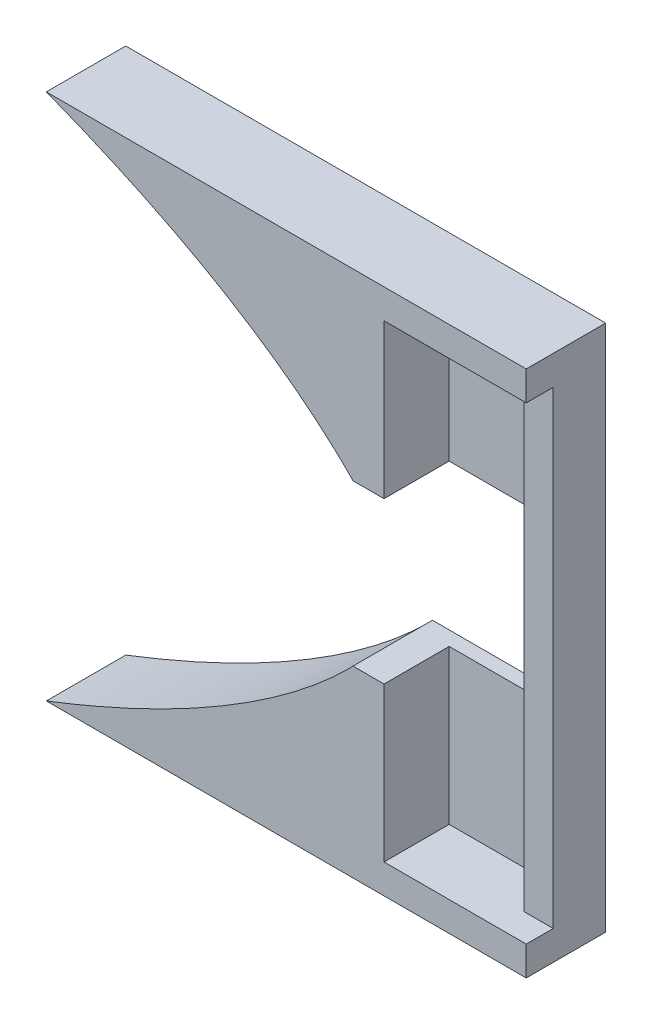
SolidWorks part; units mm, degrees
ref_plane "Front Plane" through (0, 0, 0) normal (0, 0, 1) x (1, 0, 0)
ref_plane "Top Plane" through (0, 0, 0) normal (0, 1, 0) x (1, 0, 0)
ref_plane "Right Plane" through (0, 0, 0) normal (1, 0, 0) x (0, 0, -1)
sketch "Sketch1" plane through (0, 0, 0) normal (0, 0, 1) x (1, 0, 0)
  line L0 (-3.952, 0) -> (4.2326, 0) construction
  line L1 (0, 24) -> (0, -24)
  line L2 (0, 24) -> (0, -24)
  line L3 (63, 14.75) -> (63.35, 14.75) construction
  line L4 (38.2956, -15.1) -> (63.35, -15.1)
  line L5 (38.2956, -15.1) -> (38.2956, 15.1)
  line L6 (38.2956, 15.1) -> (63.35, 15.1)
  line L7 (63.35, -15.1) -> (63.35, 15.1)
  line L8 (38.2956, -15.1) -> (63.35, 15.1) construction
  line L9 (38.2956, 15.1) -> (63.35, -15.1) construction
  line L10 (63, 14.75) -> (63, 15.1) construction
  line L11 (55.9, 5.05) -> (55.9, -5.05)
  line L12 (55.9, 14.75) -> (55.9, 5.05)
  line L13 (55.9, 5.05) -> (59.2, 5.05)
  line L14 (59.2, 5.05) -> (60.45, 5.05)
  line L15 (60.45, 5.05) -> (60.45, -5.05)
  line L16 (60.45, -5.05) -> (59.2, -5.05)
  line L17 (59.2, -5.05) -> (55.9, -5.05)
  line L18 (55.9, -5.05) -> (55.9, -14.75)
  line L19 (55.9, -14.75) -> (63, -14.75)
  line L20 (63, -14.75) -> (63, 14.75)
  line L21 (63, 14.75) -> (55.9, 14.75)
  line L22 (55.9, 14.75) -> (55.9, 5.05)
  line L23 (55.9, 5.05) -> (59.2, 5.05)
  line L24 (59.2, 5.05) -> (60.45, 5.05)
  line L25 (60.45, 5.05) -> (60.45, -5.05)
  line L26 (60.45, -5.05) -> (59.2, -5.05)
  line L27 (59.2, -5.05) -> (55.9, -5.05)
  line L28 (55.9, -5.05) -> (55.9, -14.75)
  line L29 (55.9, -14.75) -> (63, -14.75)
  line L30 (63, -14.75) -> (63, 14.75)
  line L31 (63, 14.75) -> (55.9, 14.75)
  line L32 (63.35, 15.1) -> (64.85, 15.1) construction
  line L33 (55.9, 5.05) -> (53.945, 5.05)
  line L34 (55.9, 5.05) -> (55.9, -5.05)
  line L35 (55.9, -5.05) -> (53.945, -5.05)
  line L36 (53.945, 5.05) -> (53.945, -5.05)
  line L37 (34.6449, -16.6) -> (64.85, -16.6)
  line L38 (34.6449, -16.6) -> (34.6449, 16.6)
  line L39 (34.6449, 16.6) -> (64.85, 16.6)
  line L40 (64.85, -16.6) -> (64.85, 16.6)
  line L41 (34.6449, -16.6) -> (64.85, 16.6) construction
  line L42 (34.6449, 16.6) -> (64.85, -16.6) construction
  line L43 (63.35, 15.1) -> (63.35, 16.6) construction
  arc A1 (53.7033, -5.3033) -> (53.7033, 5.3033) centre (48.4, 0) ccw
  arc A2 (53.7033, -5.3033) -> (53.7033, 5.3033) centre (48.4, 0) ccw
  spline S2 degree 3 poles (-39742.6829, -3603.7041) (40725.6647, 1982.9369) (-40729.1405, -551.1643) (39971.9091, -538.7658) knots -9.910331 -9.910331 -9.910331 -9.910331 10.871093 10.871093 10.871093 10.871093 only from (53.7033, 5.3033) to (0, 24)
  spline S3 degree 3 poles (39973.8727, 538.7655) (-40730.5107, 551.2054) (40726.4161, -1982.9853) (-39742.8292, 3603.7143) knots -9.871262 -9.871262 -9.871262 -9.871262 10.910344 10.910344 10.910344 10.910344 only from (0, -24) to (53.7033, -5.3033)
  spline S4 degree 3 poles (53.7033, 5.3033) (40.8426, 18.164) (10.9049, 24) (0, 24) knots 0 0 0 0 1 1 1 1
  spline S5 degree 3 poles (0, -24) (10.9049, -24) (40.8426, -18.164) (53.7033, -5.3033) knots 0 0 0 0 1 1 1 1
  point P16 (50.8228, 0)
  point P28 (49.7474, 0)
  dimension "D3" = 0.35
  dimension "D4" = 1.5
  dimension "D1" = 0
  dimension "D2" = 0
extrude "Boss-Extrude1" add sketch "Sketch1" against normal blind 3.3 contours S5 L4 L7 L6 S4 A2 L31 L30 L29 L28 L27 L26 L25 L24 L23 L22 | S5 L37 L40 L39 S4 L6 L7 L4
sketch "Sketch2" plane through (0, 0, -3.3) normal (0, 0, -1) x (-1, 0, 0)
  line L0 (-63, -14.75) -> (-63, 14.75) construction
  line L1 (-55.9, -14.75) -> (-63, -14.75)
  line L2 (-55.9, -14.75) -> (-55.9, -5.05)
  line L3 (-55.9, -5.05) -> (-63, -5.05)
  line L4 (-63, -14.75) -> (-63, -5.05)
  line L5 (-55.9, -5.05) -> (-53.945, -5.05) construction
  line L6 (-55.9, 5.05) -> (-53.945, 5.05) construction
  line L7 (-55.9, 14.75) -> (-63, 14.75)
  line L8 (-55.9, 14.75) -> (-55.9, 5.05)
  line L9 (-55.9, 5.05) -> (-63, 5.05)
  line L10 (-63, 14.75) -> (-63, 5.05)
extrude "Boss-Extrude2" add sketch "Sketch2" against normal blind 0.9
sketch "Sketch3" plane through (0, 0, 0) normal (0, 0, 1) x (1, 0, 0)
  line L0 (63, 14.75) -> (64.85, 14.75)
  line L1 (63, -14.75) -> (64.85, -14.75)
  line L10 (34.6449, -16.6) -> (64.85, -16.6)
  line L11 (64.85, -16.6) -> (64.85, 16.6)
  line L12 (64.85, 16.6) -> (34.6449, 16.6)
  line L13 (53.945, 5.05) -> (55.9, 5.05)
  line L14 (55.9, 5.05) -> (55.9, 14.75)
  line L15 (55.9, 14.75) -> (63, 14.75)
  line L16 (63, 14.75) -> (63, -14.75)
  line L17 (63, -14.75) -> (55.9, -14.75)
  line L18 (55.9, -14.75) -> (55.9, -5.05)
  line L19 (55.9, -5.05) -> (53.945, -5.05)
  line L20 (34.6449, -16.6) -> (64.85, -16.6)
  line L21 (64.85, -16.6) -> (64.85, 16.6)
  line L22 (64.85, 16.6) -> (34.6449, 16.6)
  line L23 (53.945, 5.05) -> (55.9, 5.05)
  line L24 (55.9, 5.05) -> (55.9, 14.75)
  line L25 (55.9, 14.75) -> (63, 14.75)
  line L26 (63, 14.75) -> (63, -14.75)
  line L27 (63, -14.75) -> (55.9, -14.75)
  line L28 (55.9, -14.75) -> (55.9, -5.05)
  line L29 (55.9, -5.05) -> (53.945, -5.05)
  arc A2 (53.945, 5.05) -> (53.7033, 5.3033) centre (48.4, 0) ccw
  arc A3 (53.7033, -5.3033) -> (53.945, -5.05) centre (48.4, 0) ccw
  arc A4 (53.945, 5.05) -> (53.7033, 5.3033) centre (48.4, 0) ccw
  arc A5 (53.7033, -5.3033) -> (53.945, -5.05) centre (48.4, 0) ccw
  spline S2 degree 3 poles (-3879.0587, 677.7435) (4374.4057, -283.8585) (-4352.4954, -64.6618) (4026.7804, 213.356) knots -3.777275 -3.777275 -3.777275 -3.777275 6.032356 6.032356 6.032356 6.032356 only from (53.7033, -5.3033) to (34.6449, -16.6)
  spline S3 degree 3 poles (4026.7948, -213.3565) (-4352.5089, 64.6617) (4374.4178, 283.8592) (-3879.0692, -677.7447) knots -5.032361 -5.032361 -5.032361 -5.032361 4.777279 4.777279 4.777279 4.777279 only from (34.6449, 16.6) to (53.7033, 5.3033)
  spline S4 degree 3 poles (53.7033, -5.3033) (49.0287, -9.9779) (42.0978, -13.7245) (34.6449, -16.6) knots 0.636517 0.636517 0.636517 0.636517 1 1 1 1
  spline S5 degree 3 poles (34.6449, 16.6) (42.0978, 13.7245) (49.0287, 9.9779) (53.7033, 5.3033) knots 0 0 0 0 0.363483 0.363483 0.363483 0.363483
  spline M15 degree 3 poles (53.7033, -5.3033) (40.8426, -18.164) (10.9049, -24) (0, -24) knots 0 0 0 0 1 1 1 1 only from (53.7033, -5.3033) to (34.6449, -16.6)
  line M16 (34.6449, -16.6) -> (64.85, -16.6)
  line M17 (64.85, -16.6) -> (64.85, 16.6)
  line M18 (64.85, 16.6) -> (34.6449, 16.6)
  spline M19 degree 3 poles (0, 24) (10.9049, 24) (40.8426, 18.164) (53.7033, 5.3033) knots 0 0 0 0 1 1 1 1 only from (34.6449, 16.6) to (53.7033, 5.3033)
  arc M20 (53.7033, 5.3033) -> (53.945, 5.05) centre (48.4, 0) cw
  line M21 (53.945, 5.05) -> (55.9, 5.05)
  line M22 (55.9, 5.05) -> (55.9, 14.75)
  line M23 (55.9, 14.75) -> (63, 14.75)
  line M25 (63, -14.75) -> (55.9, -14.75)
  line M26 (55.9, -14.75) -> (55.9, -5.05)
  line M27 (55.9, -5.05) -> (53.945, -5.05)
  arc M28 (53.945, -5.05) -> (53.7033, -5.3033) centre (48.4, 0) cw
  dimension "D1" = 0
extrude "Boss-Extrude3" add sketch "Sketch3" along normal offset from surface (1.7 mm away) 5 contours L1 M25 M26 M27 M28 M15 M16 M17 | L0 M23 M17 M18 M19 M20 M21 M22
